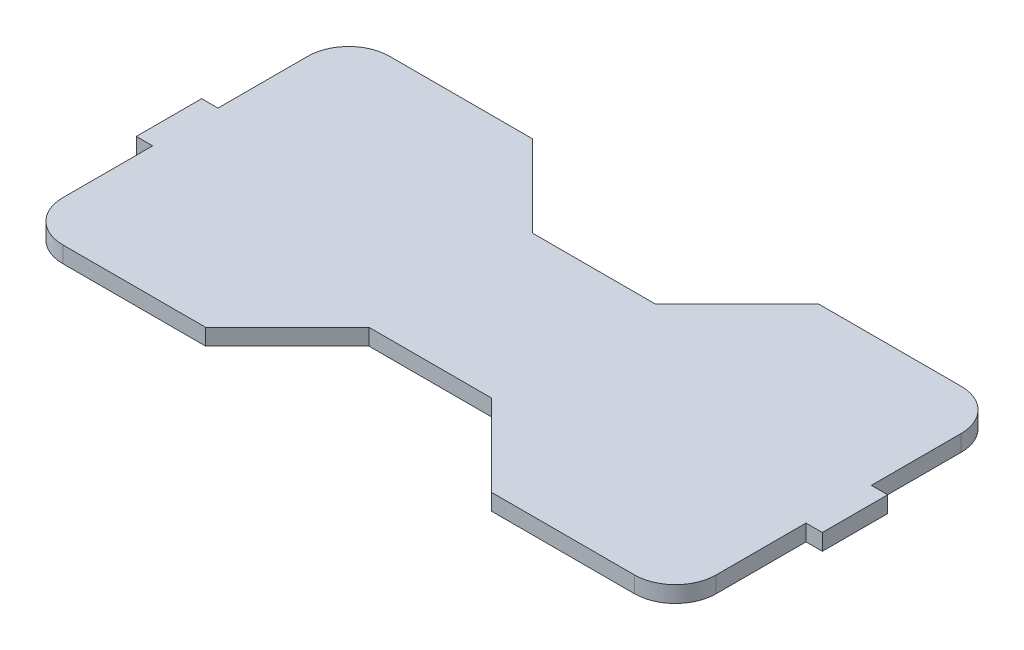
SolidWorks part; units mm, degrees
ref_plane "Front Plane" through (0, 0, 0) normal (0, 0, 1) x (1, 0, 0)
ref_plane "Top Plane" through (0, 0, 0) normal (0, 1, 0) x (1, 0, 0)
ref_plane "Right Plane" through (0, 0, 0) normal (1, 0, 0) x (0, 0, -1)
sketch "Sketch1" plane through (0, 0, 0) normal (0, 1, 0) x (1, 0, 0)
  line L0 (0, 0) -> (0, 19923.1587) construction
  line L1 (0, 0) -> (-19923.1587, 0) construction
  line L2 (-9.525, 12.7) -> (-22.225, 25.4)
  line L3 (-22.225, 25.4) -> (-50.8, 25.4)
  line L4 (-50.8, 25.4) -> (-50.8, 5.08)
  line L5 (-50.8, 5.08) -> (-53.34, 5.08)
  line L6 (-53.34, 5.08) -> (-53.34, -5.08)
  line L8 (22.225, 25.4) -> (50.8, 25.4)
  line L9 (50.8, 25.4) -> (50.8, 5.08)
  line L10 (50.8, 5.08) -> (53.34, 5.08)
  line L11 (53.34, 5.08) -> (53.34, -5.08)
  line L12 (50.8, -5.08) -> (53.34, -5.08)
  line L13 (50.8, -25.4) -> (50.8, -5.08)
  line L14 (22.225, -25.4) -> (50.8, -25.4)
  line L16 (-9.525, -12.7) -> (-22.225, -25.4)
  line L17 (-22.225, -25.4) -> (-50.8, -25.4)
  line L18 (-50.8, -25.4) -> (-50.8, -5.08)
  line L19 (-50.8, -5.08) -> (-53.34, -5.08)
  line L20 (-9.525, 12.7) -> (9.525, 12.7)
  line L21 (9.525, 12.7) -> (22.225, 25.4)
  line L22 (9.525, -12.7) -> (22.225, -25.4)
  line L23 (-9.525, -12.7) -> (9.525, -12.7)
  point P17 (53.34, 0)
  point P25 (-53.34, 0)
  point P26 (0, 12.7)
  dimension "D1" = 25.4
  dimension "D2" = 50.8
  dimension "D3" = 2.54
  dimension "D4" = 5.08
  dimension "D5" = 45
  dimension "D6" = 12.7
  dimension "D7" = 19.05
extrude "Boss-Extrude1" add sketch "Sketch1" along normal blind 2.54 contours L3 L4 L5 L6 L19 L18 L17 L16 L23 L22 L14 L13 L12 L11 L10 L9 L8 L21 L20 L2
fillet "Fillet1" radius 6.35 4 edges at (50.8, 1.27, -25.4) (50.8, 1.27, 25.4) (-50.8, 1.27, -25.4) (-50.8, 1.27, 25.4)
sketch "Sketch2" plane through (0, 2.54, 0) normal (0, 1, 0) x (1, 0, 0)
  point P0 (0, 0)
  point P1 (2.6136, 22.9064)
